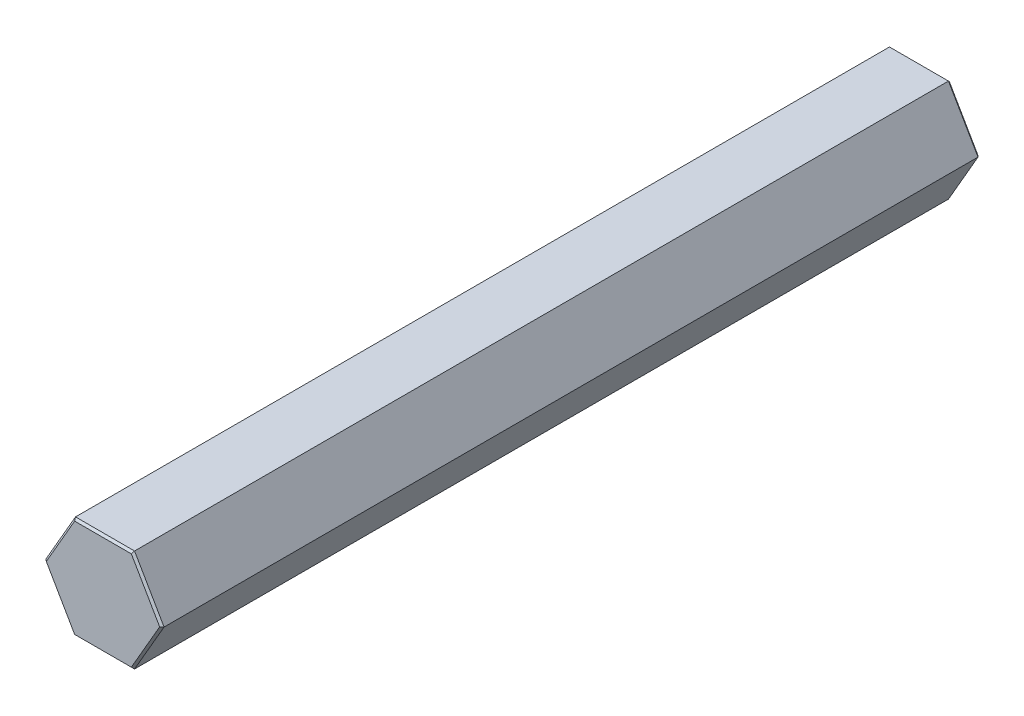
SolidWorks part; units mm, degrees
material "1060 Alloy"
ref_plane "Front Plane" through (0, 0, 0) normal (0, 0, 1) x (1, 0, 0)
ref_plane "Top Plane" through (0, 0, 0) normal (0, 1, 0) x (1, 0, 0)
ref_plane "Right Plane" through (0, 0, 0) normal (1, 0, 0) x (0, 0, -1)
ref_plane "Plane1" through (0, 0, 0) normal (0, 0, -1) x (-1, 0, 0)
sketch "Sketch1" plane through (0, 0, 0) normal (0, 0, -1) x (-1, 0, 0)
  line L0 (3.6662, 6.35) -> (-3.6662, 6.35)
  line L1 (-3.6662, 6.35) -> (-7.3323, 0)
  line L2 (-7.3323, 0) -> (-3.6662, -6.35)
  line L3 (-3.6662, -6.35) -> (3.6662, -6.35)
  line L4 (3.6662, -6.35) -> (7.3323, 0)
  line L5 (7.3323, 0) -> (3.6662, 6.35)
extrude "Boss-Extrude1" add sketch "Sketch1" against normal blind 101.6
chamfer "Chamfer1" distance 0.254 angle 45 12 edges at (0, -6.35, 0) (5.4993, -3.175, 0) (-5.4993, -3.175, 0) (5.4993, 3.175, 0) (-5.4993, 3.175, 0) (0, 6.35, 0) (-5.4993, -3.175, 101.6) (0, -6.35, 101.6) (-5.4993, 3.175, 101.6) (5.4993, -3.175, 101.6) (0, 6.35, 101.6) (5.4993, 3.175, 101.6)
